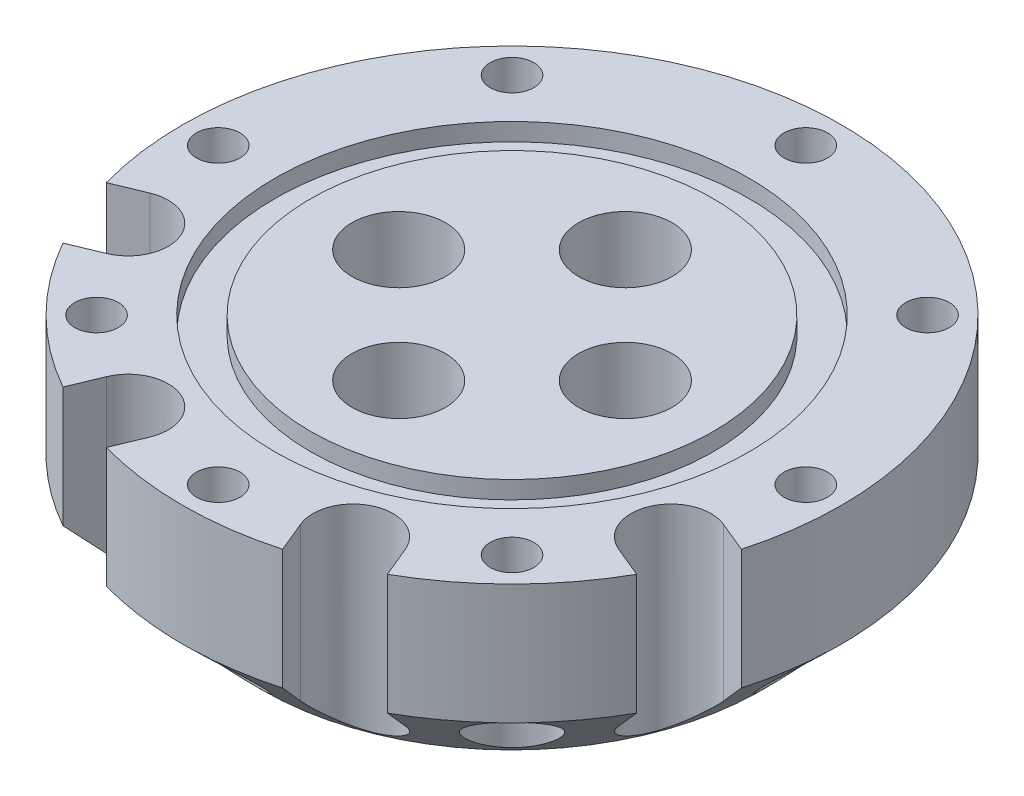
SolidWorks part; units mm, degrees
other "DetailItem1"
other "DetailItem2"
material "6061-T6 (SS)"
ref_plane "Front Plane" through (0, 0, 0) normal (0, 0, 1) x (1, 0, 0)
ref_plane "Top Plane" through (0, 0, 0) normal (0, 1, 0) x (1, 0, 0)
ref_plane "Right Plane" through (0, 0, 0) normal (1, 0, 0) x (0, 0, -1)
sketch "Sketch1" plane through (0, 0, 0) normal (0, 1, 0) x (1, 0, 0)
  circle A0 centre (0, 0) radius 24.675
  dimension "D1" = 49.35
extrude "Boss-Extrude1" add sketch "Sketch1" against normal blind 15
sketch "Sketch2" plane through (0, -15, 0) normal (0, -1, 0) x (1, 0, 0)
  line L0 (0, -8.4853) -> (-8.4853, 0) construction
  line L1 (0, -8.4853) -> (8.4853, 0) construction
  line L2 (-8.4853, 0) -> (0, 8.4853) construction
  line L3 (8.4853, 0) -> (0, 8.4853) construction
  line L4 (0, -8.4853) -> (0, 8.4853) construction
  line L5 (-8.4853, 0) -> (8.4853, 0) construction
  circle A0 centre (0, 8.4853) radius 3.5
  circle A1 centre (-8.4853, 0) radius 3.5
  circle A2 centre (0, -8.4853) radius 3.5
  circle A3 centre (8.4853, 0) radius 3.5
  point P1 (0, 0)
  dimension "D2" = 7
  dimension "D1" = 12
extrude "Cut-Extrude1" cut sketch "Sketch2" against normal blind 15
sketch "Sketch3" plane through (0, 0, 0) normal (0, 1, 0) x (1, 0, 0)
  circle A0 centre (0, 0) radius 15.0876
  circle A1 centre (0, 0) radius 17.7546
  dimension "D1" = 2.667
  dimension "D2" = 30.1752
extrude "Cut-Extrude2" cut sketch "Sketch3" against normal blind 1.3208
chamfer "Chamfer1" distance 6 angle 45 1 edges at (0, -15, 24.675)
sketch "Sketch4" plane through (0, -15, 0) normal (0, -1, 0) x (1, 0, 0)
  line L0 (0, 0) -> (0, 22) construction
  point P4 (0, 22)
  dimension "D1" = 22
hole_wizard "CBORE for #4 Button Head Cap Screw1" positions "Sketch5" profile "Sketch7" counterbore size "#4" standard "ANSI Inch"
sketch "Sketch5" plane through (0, -15, 0) normal (0, -1, 0) x (-1, 0, 0)
  point P0 (0, -22)
sketch "Sketch7" plane through (0, -15, 22) normal (1, 0, 0) x (0, 0, -1)
  line L0 (0, 0) -> (0, 15)
  line L1 (0, 15) -> (1.6319, 15)
  line L3 (1.6319, 15) -> (1.6319, 6)
  line L4 (1.6319, 6) -> (2.794, 6)
  line L5 (2.794, 6) -> (2.794, 0)
  line L7 (2.794, 0) -> (0, 0)
  line L11 (0, -6.35) -> (0, 107.95) construction
  dimension "Thru Hole Dia." = 3.2639
  dimension "Thru Hole Depth" = 15
  dimension "C'Bore Dia." = 5.588
  dimension "C'Bore Depth" = 6
pattern_circular "CirPattern1" count 8 over 360 about axis through (0, 0, 0) along (0, 1, 0) of "CBORE for #4 Button Head Cap Screw1"
sketch "Sketch8" plane through (0, -15, 0) normal (0, -1, 0) x (1, 0, 0)
  line L0 (0, 0) -> (8.419, 20.3253) construction
  line L1 (0, 0) -> (0, 22) construction
  line L2 (21.4734, 5.6474) -> (23.7757, 6.601)
  line L3 (0, 0) -> (0, 22) construction
  line L4 (8.419, 20.3253) -> (11.1907, 19.1773) construction
  line L5 (11.1907, 19.1773) -> (12.1443, 21.4796)
  line L6 (5.6474, 21.4734) -> (6.601, 23.7757)
  line L7 (19.1773, 11.1907) -> (21.4796, 12.1443)
  line L8 (-21.4734, 5.6474) -> (-23.7757, 6.601)
  line L9 (0, 0) -> (20.3253, 8.419) construction
  line L10 (-19.1773, 11.1907) -> (-21.4796, 12.1443)
  line L11 (-5.6474, 21.4734) -> (-6.601, 23.7757)
  line L12 (-11.1907, 19.1773) -> (-12.1443, 21.4796)
  arc A0 (5.6474, 21.4734) -> (11.1907, 19.1773) centre (8.419, 20.3253) ccw
  circle A2 centre (0, 0) radius 24.675 construction
  circle A3 centre (0, 0) radius 24.675
  arc A4 (19.1773, 11.1907) -> (21.4734, 5.6474) centre (20.3253, 8.419) ccw
  arc A5 (-19.1773, 11.1907) -> (-21.4734, 5.6474) centre (-20.3253, 8.419) cw
  arc A6 (-5.6474, 21.4734) -> (-11.1907, 19.1773) centre (-8.419, 20.3253) cw
  dimension "D4" = 3
  dimension "D1" = 22
  dimension "D2" = 22.5
  dimension "D3" = 2
  dimension "D5" = 67.5
extrude "Cut-Extrude3" cut sketch "Sketch8" against normal through all contours L7 A4 L2 A3 | L5 A3 L6 A0 | A6 L11 A3 L12 | A5 L10 A3 L8
chamfer "Chamfer2" distance 0.3 angle 45 4 edges at (-8.4853, -15, -3.5) (0, -15, -11.9853) (8.4853, -15, -3.5) (0, -15, 4.9853)
